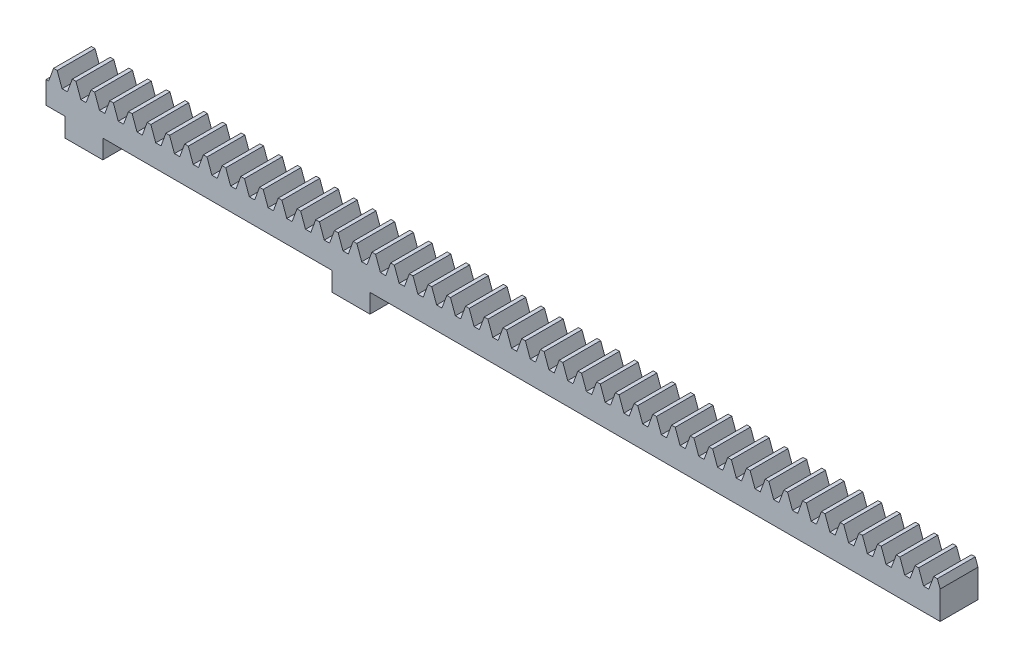
SolidWorks part; units mm, degrees
ref_plane "Plane1" through (0, 0, 0) normal (0, 0, 1) x (1, 0, 0)
ref_plane "Plane2" through (0, 0, 0) normal (0, 1, 0) x (1, 0, 0)
ref_plane "Plane3" through (0, 0, 0) normal (1, 0, 0) x (0, 0, -1)
sketch "HoldingSke" plane through (0, 0, 0) normal (0, 1, 0) x (1, 0, 0)
  line L0 (0, 0) -> (0.1392, 0.9903)
  line L1 (-15, 0) -> (100, 0) construction
  line L2 (0, 0) -> (-2.1039, 2.3779)
  line L3 (0, 0) -> (-11.863, 4.5341)
  line L4 (0, 0) -> (5.6657, 6.5177)
  line L5 (0, 0) -> (-23.7986, -8.8762)
  line L6 (0, 0) -> (-10.5278, -7.1032)
  line L9 (-71.009, 38.7566) -> (69.9449, 90.0596)
  line L10 (-76.2, 3.3779) -> (-71.2, 3.3779)
  line L11 (0, 0) -> (-6.35, 0)
  line L12 (-76.2, 101.6) -> (-76.162, 101.6)
  line L13 (24.9733, 27.94) -> (52.9518, 28.4284)
  line L14 (24.9733, 27.94) -> (24.9743, 27.94)
  line L15 (24.9733, 27.94) -> (100.4006, 29.5858)
  circle A0 centre (0, 0) radius 19.05
  circle A1 centre (0, 0) radius 2.5
  circle A2 centre (0, 0) radius 12.7
  dimension "MPH" = 5
  dimension "Diameter" = 38.1
  dimension "Num_teeth" = 49
  dimension "Pitch" = 1
  dimension "Width" = 6.35
  dimension "Show_teeth" = 998
  dimension "Thickness" = 12.7
  dimension "Ap" = 20
  dimension "Pitch_height" = 5
  dimension "Backlash" = 0.038
  dimension "Addendum_fac" = 1
  dimension "Dedendum_fac" = 1.25
  dimension "Clearance_fac" = 0.25
  dimension "Dedendum_add" = 0.001
  dimension "Length" = 150
  dimension "Module" = 1
sketch "BlankSke" plane through (0, 0, 0) normal (0, 0, 1) x (1, 0, 0)
  line L1 (0, 0) -> (150, 0)
  line L2 (0, 0) -> (0, 6)
  line L3 (0, 6) -> (150, 6)
  line L4 (150, 0) -> (150, 6)
  dimension "Length" = 150
  dimension "Blank_height" = 6
extrude "Blank" add sketch "BlankSke" against normal blind 6.35
sketch "TooCutSkeIll" plane through (0, 0, 0) normal (0, 0, 1) x (1, 0, 0)
  line L0 (-1.2538, 5.9737) -> (-0.5045, 3.9152)
  line L1 (-0.2687, 3.75) -> (0.2687, 3.75)
  line L2 (0.5045, 3.9152) -> (1.2538, 5.9737)
  line L3 (150, 6) -> (0, 6) construction
  line L4 (0, 0) -> (0, 64.897) construction
  line L5 (-13.208, 5) -> (12.954, 5) construction
  line L6 (0, 0) -> (150, 0) construction
  line L7 (0.8994, 5) -> (0.8994, 48.7463) construction
  line L8 (-0.8994, 5) -> (-0.8994, 48.7463) construction
  line L9 (1.2914, 6) -> (1.2914, 6.0254)
  line L10 (-1.2914, 6) -> (-1.2914, 6.0254)
  line L11 (-1.2914, 6.0254) -> (1.2914, 6.0254)
  arc A0 (0.2687, 3.75) -> (0.5045, 3.9152) centre (0.2687, 4.001) ccw
  arc A1 (-0.5045, 3.9152) -> (-0.2687, 3.75) centre (-0.2687, 4.001) ccw
  arc A2 (1.2914, 6) -> (1.2538, 5.9737) centre (1.2914, 5.96) ccw
  arc A3 (-1.2538, 5.9737) -> (-1.2914, 6) centre (-1.2914, 5.96) ccw
  dimension "Root_fillet" = 0.251
  dimension "Break_rad" = 0.04
  dimension "Pitch_height" = 5
  dimension "Gap_width" = 1.7988
  dimension "Dedendum" = 1.25
  dimension "Addendum_plus" = 1.0254
  dimension "Pressure_angle" = 20
extrude "ToothCutIll" [suppressed] cut sketch "TooCutSkeIll" against normal through all
sketch "TooCutSkeSim" plane through (0, 0, 0) normal (0, 0, 1) x (1, 0, 0)
  line L0 (0.4444, 3.75) -> (-0.4444, 3.75)
  line L1 (1.2726, 6.0254) -> (0.4444, 3.75)
  line L2 (0, 17.4625) -> (0, 53.467) construction
  line L3 (1.2726, 6.0254) -> (-1.2726, 6.0254)
  line L6 (-1.2726, 6.0254) -> (-0.4444, 3.75)
  line L9 (-0.8994, 5) -> (0.8994, 5) construction
  line L10 (0, 0) -> (150, 0) construction
  line L11 (0.8994, 5) -> (0.8994, 53.467) construction
  line L12 (-0.8994, 5) -> (-0.8994, 53.467) construction
  dimension "Pitch_height" = 5
  dimension "Pressure_angle" = 20
  dimension "Gap_width" = 1.7988
  dimension "Dedendum" = 1.25
  dimension "Addendum_plus" = 1.0254
extrude "ToothCutSim" cut sketch "TooCutSkeSim" against normal through all
pattern_linear "TeethCuts" count 48 spacing 3.1416 along (1, 0, 0) of "ToothCutIll", "ToothCutSim"
sketch "Sketch1" plane through (0, 0, 0) normal (0, -1, 0) x (1, 0, 0)
  line L0 (48, 0) -> (48, -6.35)
  line L1 (48, 0) -> (54.35, 0)
  line L2 (48, -6.35) -> (54.35, -6.35)
  line L3 (54.35, 0) -> (54.35, -6.35)
  line L6 (0, -6.35) -> (0, 0) construction
  line L7 (0, 0) -> (150, 0) construction
  line L8 (0, -6.35) -> (150, -6.35) construction
  line L9 (3.175, 0) -> (3.175, -6.35)
  line L10 (3.175, 0) -> (9.525, 0)
  line L11 (3.175, -6.35) -> (9.525, -6.35)
  line L12 (9.525, 0) -> (9.525, -6.35)
  dimension "D1" = 48
  dimension "D2" = 6.35
  dimension "D3" = 3.175
  dimension "D4" = 6.35
extrude "ElasticPegs_Extrude" add sketch "Sketch1" along normal blind 3.175
equation "' \"Module@HoldingSke\" = 6.35"
equation "' \"Num_teeth@HoldingSke\" = 12"
equation "' \"Ap@HoldingSke\" =  20"
equation "' \"Width@HoldingSke\" = 0.25 * 25.4"
equation "' \"Show_teeth@HoldingSke\" = 500"
equation "' \"Backlash@HoldingSke\" = 0.009 * 25.4"
equation "' \"Addendum_fac@HoldingSke\" = 1.0"
equation "' \"Dedendum_fac@HoldingSke\" = 1.25"
equation "' \"Dedendum_add@HoldingSke\" = 0.00005 * 25.4"
equation "' \"Clearance_fac@HoldingSke\" = 0.25"
equation "' \"Pitch_height@HoldingSke\" = 1 * 25.4"
equation "' \"Length@HoldingSke\" = 4.71 * 25.4"
equation "\"Pitch@HoldingSke\" = 1 / \"Module@HoldingSke\""
equation "\"MPH@HoldingSke\" = \"Dedendum_fac@HoldingSke\" / \"Pitch@HoldingSke\" + 2 * \"Dedendum_add@HoldingSke\" + 0.002 * 25.4"
equation "\"MPH@HoldingSke\" = ((sgn( \"MPH@HoldingSke\" - \"Pitch_height@HoldingSke\")+1)*( \"MPH@HoldingSke\" - \"Pitch_height@HoldingSke\"))/2 + \"Pitch_height@HoldingSke\""
equation "\"Blank_height@BlankSke\" = \"Pitch_height@HoldingSke\" + \"Addendum_fac@HoldingSke\"  / \"Pitch@HoldingSke\" "
equation "\"Length@BlankSke\" =  \"Length@HoldingSke\""
equation "\"Face_width@Blank\" = \"Width@HoldingSke\""
equation "\"Pressure_angle@TooCutSkeIll\" = \"Ap@HoldingSke\""
equation "\"Addendum_plus@TooCutSkeIll\" =  \"Addendum_fac@HoldingSke\"  / \"Pitch@HoldingSke\" + 0.001 *25.4"
equation "\"Dedendum@TooCutSkeIll\" = \"Dedendum_fac@HoldingSke\"  / \"Pitch@HoldingSke\""
equation "\"Pitch_height@TooCutSkeIll\" =  \"MPH@HoldingSke\""
equation "\"Gap_width@TooCutSkeIll\" = 3.14159265 / 2 / \"Pitch@HoldingSke\" + 6 * \"Backlash@HoldingSke\""
equation "\"Pressure_angle@TooCutSkeSim\" = \"Ap@HoldingSke\""
equation "\"Addendum_plus@TooCutSkeSim\" =  \"Addendum_fac@HoldingSke\"  / \"Pitch@HoldingSke\" + 0.001 * 25.4"
equation "\"Dedendum@TooCutSkeSim\" = \"Dedendum_fac@HoldingSke\"  / \"Pitch@HoldingSke\""
equation "\"Pitch_height@TooCutSkeSim\" =  \"MPH@HoldingSke\""
equation "\"Gap_width@TooCutSkeSim\" = 3.14159265 / 2 / \"Pitch@HoldingSke\" + 6 * \"Backlash@HoldingSke\""
equation "\"Root_fillet@TooCutSkeIll\" = \"Clearance_fac@HoldingSke\" / \"Pitch@HoldingSke\" + \"Dedendum_add@HoldingSke\""
equation "\"Break_rad@TooCutSkeIll\" = 0.02 / \"Pitch@HoldingSke\" * 2"
equation "\"Linear_pitch@TeethCuts\" = 3.14159265 / \"Pitch@HoldingSke\""
equation "\"Num_teeth@HoldingSke\" = int( ( \"Length@HoldingSke\" + 0 ) / (3.14159265 / \"Pitch@HoldingSke\")) + 0.9999  + 1"
equation " \"Num_teeth@TeethCuts\" = int( \"Show_teeth@HoldingSke\" ) + 1"
equation " \"Num_teeth@TeethCuts\" = ((sgn( \"Num_teeth@TeethCuts\" - \"Num_teeth@HoldingSke\" )-1)*( \"Num_teeth@TeethCuts\" - \"Num_teeth@HoldingSke\" ))/-2+ \"Num_teeth@HoldingSke\""
equation " \"Num_teeth@TeethCuts\" = ((sgn( \"Num_teeth@TeethCuts\" - 2.0)+1)*( \"Num_teeth@TeethCuts\" - 2.0))/2 +2.0"
equation "\"CageLeftBottomEdge\"=22.11mm"
equation "\"CageLeftTopEdge\"=22.11mm"
equation "\"CageRightBottomEdge\"=21.63mm"
equation "\"CageRightTopEdge\"=21.63mm"
equation "\"CageHeight\"=86.04mm"
equation "\"CageLength\"=73.76mm"
equation "\"CageTopScrewClearance\"=10mm"
equation "\"CageBottomScrewClearance\"=25mm"
equation "\"CageLeftTopDepth\"= 11.65mm"
equation "\"CageLeftBottomDepth\"=11.11mm"
equation "\"CageLeftTopHeight\"=8.56175mm"
equation "\"CageLeftBottomHeight\"=16mm"
equation "\"CageRightTopDepth\"= 11.05mm"
equation "\"CageRightBottomDepth\"=10.58mm"
equation "\"CageRightTopHeight\"=9.6mm"
equation "\"CageRightBottomHeight\"=15.49mm"
equation "\"CageLeftTopChannelDepth\"=2.41908mm"
equation "\"CageLeftBottomChannelDepth\"=2.588mm"
equation "\"CageLeftChannelHeight\"=11.7mm"
equation "\"CageRightTopChannelDepth\"=2.32mm"
equation "\"CageRightBottomChannelDepth\"=2.318mm"
equation "\"CageRightChannelHeight\"=10mm"
equation "\"CageChanRelHeight\"=23.99mm"
equation "\"CageChanRelDepth\"=5.492mm"
equation "\"CageChamberRadius\"=16.261mm"
equation "\"CageScrewDiameter\"=4.8mm"
equation "\"CageSetScrewDiameter\"=3.5mm"
equation "\"CageAxleRadius\"=6.639mm"
equation "\"CageAxleKeyHeight\"=1.619mm"
equation "\"CageAxleKeyWidth\"=2.662mm"
equation "\"CageHoseWindowWidth\"=16.29mm"
equation "\"CageHoseWindowHeight\"=26.5mm"
equation "\"CageHoseWindow-Edge\"=8.89mm"
equation "\"CageScrew-VerticalEdge\"=5.0mm"
equation "\"CageScrew-HorizontalEdge\"=7.5mm"
equation "\"CageScrew-HoseCornerScrewEdge\"=4.45mm"
equation "\"CageAxle-BottomEdge\"=56.05mm"
equation "\"CageAxle-FrontEdge\"=46.03mm"
equation "\"CageBackSetScrew-Axle\"=40mm"
equation "\"CageFrontSetScrew-Axle\"=22mm"
equation "\"CageVelocityWindow-BackEdge\"=34.8mm"
equation "\"CageVelocityWindow-BottomEdge\"=27.55mm"
equation "\"CageVelocityWindowHeight\"=22.29mm"
equation "\"CageVelocityWindowWidth\"=12.61mm"
equation "\"TriggerSlot-BottomEdge\"=6.35mm"
equation "\"TriggerSlot-FrontEdge\"=15mm"
equation "\"TriggerSlotSize\"=6.7mm"
equation "\"TriggerRackOffset\"=.236224in"
equation "\"TriggerSlotSizeInt\"=.25in"
equation "\"MotorMountLegLength\"=.25in"
equation "\"GearOffset\"=.264907in"
equation "\"TriggerSlotSpacing\"=.25in"
equation "\"TriggerMiniSlotWidth\"=3.5mm"
equation "\"TriggerRackWidth\"=6.5mm"
equation "\"whitemotordepth\"=11.27mm"
equation "\"whitemotorbackdepth\"=3.845mm"
equation "\"whitemotoraxledepth\" = 3.5mm"
equation "\"whitemotoraxleoffset\"=11.4mm"
equation "\"whitemotorwidth\"=12.07mm"
equation "\"whitemotorheight\"=16.68mm"
equation "\"whitemotorcylinderlength\" =13.04mm"
equation "\"whitemotorcylinderradius\"=3.845mm"
equation "\"whitemotorcylinderoffset\"=2.35mm"
equation "\"whitemotorcutoutlength\"=1.88mm"
equation "\"whitemotorouterrad\"=5mm"
equation "\"whitemotorinnerrad\"=2.95mm"
equation "\"elasticracklength\"=2in"
equation "\"elasticrackpegsize\"=.25in"
equation "\"elasticrackpegbuffer\"=.125in"
equation "\"elasticrackpegspacing\"=1.76476378in"
equation "\"elasticbaybuffer\"=.25in"
equation "\"elasticdepth\"=.125in"
equation "\"elasticbaydepth\"=.75in"
equation "\"motormountwidth\"=12mm"
equation "\"motormountcornerfillet\"=3mm"
equation "\"D2@Sketch1\"=\"elasticrackpegsize\""
equation "\"D4@Sketch1\"=\"elasticrackpegsize\""
equation "\"D3@Sketch1\"=\"elasticrackpegsize\"/2"
equation "\"D1@Sketch1\"=\"elasticrackpegspacing\"+\"elasticrackpegsize\"/2"
equation "\"pandiscradius\"=14in"
equation "\"towermaterialwidth\"=.25in"
equation "\"towerslotlength\"=.5in"
equation "\"towermarkerspace\"=5in"
equation "\"towerslothorizoffset\"=1in"
equation "\"towerslothorizspacing\"=2in"
equation "\"towerslotvertoffset\"=3in"
equation "\"towerslotvertspacing\"=1in"
equation "\"towerheight\"=12in"
equation "\"towerupslot\"=1in"
equation "\"toweraxle\"=.5in"
equation "\"stepperouterrad\"=10mm"
equation "\"stepperscrewsize\"=3.45mm"
equation "\"stepperscrewc2c\"=49.5mm"
equation "\"stepperdepthoffset\"=24mm"
equation "\"stepperhorizoffset\"=22.91mm"
equation "\"shaftslotOD\"=18.8mm"
equation "\"shaftslotID\"=13.28mm"
equation "\"shaftkeywidth\"=2.67mm"
equation "\"shaftkeydepth\"=1.8mm"
equation "\"shaftcollartotaldepth\"=12.5mm"
equation "\"shaftsquaredepth\"=6mm"
equation "\"shaftsetscrewsize\"=3.5mm"
equation "\"shaftkeytightdepth\"=1.85mm"
equation "\"shaftslottightID\"=12.78mm"
equation "\"shaftsetscrewoffset\"=9mm"
equation "\"cagecollartotaldepth\"=10mm"
equation "\"cagecollartotalwidth\"=35mm"
equation "\"cagecollarbasedepth\"=4mm"
equation "\"gearhubintdiam\"=30mm"
equation "\"gearhubintwid\"=15mm"
equation "\"towerspeedwidth\"=2in"
equation "\"towerspeedheight\"=8in"
equation "\"towerspeedgap\"=2in"
equation "\"stepperaxleflat\"=.037in"
equation "\"stepperaxlerad\"=0.11811024in"
equation "\"ajaxaxlesize\"=3.87mm"
equation "\"ajaxinnercut\"=2.3mm"
equation "\"ajaxwidth\"=6.1mm"
equation "\"ajaxdiametral\"=25.8854"
equation "\"ajaxcutoutdepth\"=2.3mm"
equation "\"ajax4020gap\"=29.5mm"
equation "\"ajax4010gap\"=24.5mm"
equation "\"ajax20hubbuffer\"=0.240157in"
equation "\"ajax20hubholeoffset\"=.19685in"
equation "\"ajax20hubholesize\"=.059055in"
equation "\"ajax20cutoutint\"=13.4mm"
equation "\"ajax40hubholesize\"=7.21mm"
equation "\"ajax40hubholeoffset\"=10mm"
equation "\"ajax40hubbuffer\"=.350394in"
equation "\"ajax40cutoutint\"=32.6mm"
equation "\"bearingpandiscrad\"=6.8in"
equation "\"bearingpandiscang\"=48.75deg"
equation "\"bearingclearholedist\"=4.7345in"
equation "\"bearingclearholesize\"=.5in"
equation "\"bearingclearholeang\"=22.5deg"
equation "\"bearingmountholedist\"=4.25in"
equation "\"bearingwirehole\"=1.5in"
equation "\"no6diam\"=.146in"
equation "\"shortconangle\"=20deg"
equation "\"shortconlen\"=.875in"
equation "\"longconlen\"=1.25in"
equation "\"longconangle\"=15deg"
equation "\"TGMGearFaceDiameter\"=24.40mm"
equation "\"TGMCylinderLength\"=15.00mm"
equation "\"TGMScrewHole-Center\"=8.70mm"
equation "\"TGMScrewHoleDiameter\"=5.04mm"
equation "\"TGMCenterHoleDiameter\"=9.50mm"
equation "\"TGMShaftCollarSideLength\"=19.00mm"
equation "\"TGMShaftCollarDockingDepth\"=7.00mm"
equation "\"towerplatslotoffset\"=1.5in"
equation "\"towermotorpanelheight\"=10in"
equation "\"towerplatdepth\"=2in"
equation "\"ajaxhubdepth\"=.25in"
equation "\"shconangle\"=20deg"
equation "\"shconlen\"=1in"
equation "\"lnconlen\"=1.5in"
equation "\"lnconangle\"=15deg"
